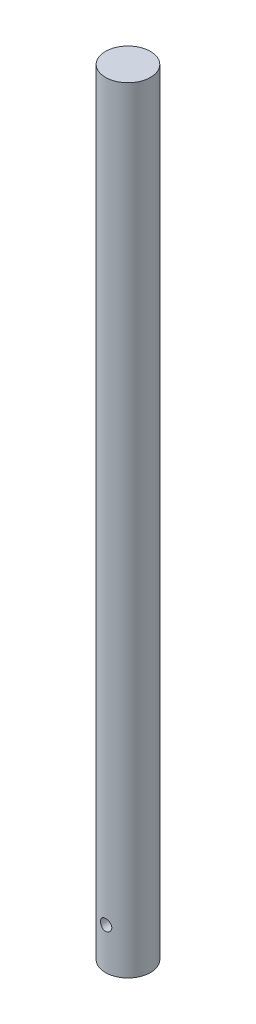
SolidWorks part; units mm, degrees
material "AISI 1020"
ref_plane "Alzado" through (0, 0, 0) normal (0, 0, 1) x (1, 0, 0)
ref_plane "Planta" through (0, 0, 0) normal (0, 1, 0) x (1, 0, 0)
ref_plane "Vista lateral" through (0, 0, 0) normal (1, 0, 0) x (0, 0, -1)
sketch "Croquis4" plane through (0, 0, 0) normal (0, 1, 0) x (1, 0, 0)
  circle A0 centre (0, 0) radius 19.05
  dimension "D1" = 38.1
extrude "Saliente-Extruir2" add sketch "Croquis4" along normal blind 656.12
sketch "Croquis5" plane through (0, 0, 0) normal (0, 0, 1) x (1, 0, 0)
  circle A0 centre (0, 35) radius 4.765
  dimension "D1" = 9.53
  dimension "35" = 35
extrude "Cortar-Extruir2" cut sketch "Croquis5" against normal through all both and the other way through all
